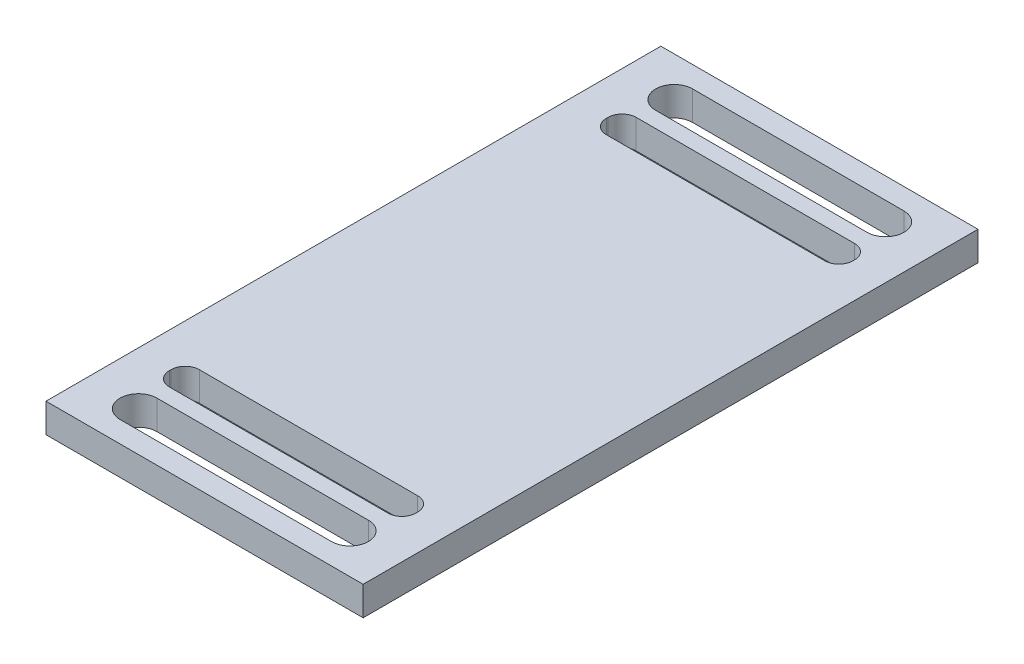
SolidWorks part; units mm, degrees
material "PVC hart"
ref_plane "Ebene vorne" through (0, 0, 0) normal (0, 0, 1) x (1, 0, 0)
ref_plane "Ebene oben" through (0, 0, 0) normal (0, 1, 0) x (1, 0, 0)
ref_plane "Ebene rechts" through (0, 0, 0) normal (1, 0, 0) x (0, 0, -1)
sketch "Skizze1" plane through (0, 0, 0) normal (0, 1, 0) x (1, 0, 0)
  line L0 (-9, 0) -> (9, 0) construction
  line L1 (-9, 17.45) -> (9, 17.45)
  line L2 (-9, 17.45) -> (-9, -17.45)
  line L3 (-9, -17.45) -> (9, -17.45)
  line L4 (9, 17.45) -> (9, -17.45)
  line L5 (-6, -15.2) -> (6, -15.2) construction
  line L6 (-7, 13.25) -> (7, 13.25)
  line L7 (-7, 13.25) -> (-7, 11.55)
  line L8 (-7, 11.55) -> (7, 11.55)
  line L9 (7, 13.25) -> (7, 11.55)
  line L10 (-6, 15.2) -> (6, 15.2) construction
  line L11 (-6, 16.25) -> (6, 16.25)
  line L12 (-6, 14.15) -> (6, 14.15)
  line L13 (0, 0) -> (0, 13.25) construction
  line L14 (0, 15.2) -> (0, 0) construction
  line L15 (-6, -16.25) -> (6, -16.25)
  line L16 (-6, -14.15) -> (6, -14.15)
  line L17 (7, -13.25) -> (7, -11.55)
  line L18 (-7, -11.55) -> (7, -11.55)
  line L19 (-7, -13.25) -> (-7, -11.55)
  line L20 (-7, -13.25) -> (7, -13.25)
  arc A0 (-6, 16.25) -> (-6, 14.15) centre (-6, 15.2) ccw
  arc A1 (6, 14.15) -> (6, 16.25) centre (6, 15.2) ccw
  arc A2 (-6, -16.25) -> (-6, -14.15) centre (-6, -15.2) cw
  arc A3 (6, -14.15) -> (6, -16.25) centre (6, -15.2) cw
  point P14 (0, 15.2)
  point P21 (0, -15.2)
  dimension "D5" = 4.2
  dimension "D6" = 12
  dimension "D7" = 1.05
  dimension "D8" = 2.25
  dimension "D1" = 18
  dimension "D2" = 14
  dimension "D3" = 1.7
  dimension "D4" = 26.5
extrude "Aufsatz-Linear austragen1" add sketch "Skizze1" against normal mid plane 1.65
fillet "Verrundung1" radius 0.8 8 edges at (7, 0, -13.25) (7, 0, -11.55) (-7, 0, -11.55) (-7, 0, -13.25) (7, 0, 13.25) (7, 0, 11.55) (-7, 0, 13.25) (-7, 0, 11.55)
